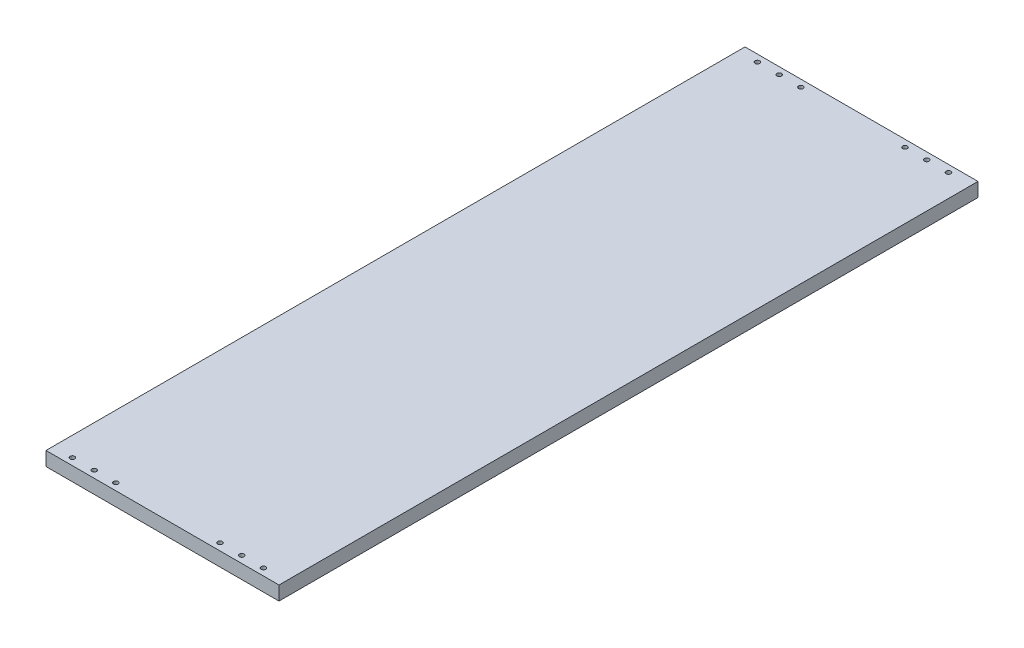
SolidWorks part; units mm, degrees
ref_plane "Спереди" through (0, 0, 0) normal (0, 0, 1) x (1, 0, 0)
ref_plane "Сверху" through (0, 0, 0) normal (0, 1, 0) x (1, 0, 0)
ref_plane "Справа" through (0, 0, 0) normal (1, 0, 0) x (0, 0, -1)
sketch "Эскиз2" plane through (0, 0, 0) normal (0, 1, 0) x (1, 0, 0)
  line L1 (0, 0) -> (300, 0)
  line L2 (0, 0) -> (0, 900)
  line L3 (0, 900) -> (300, 900)
  line L4 (300, 0) -> (300, 900)
extrude "Бобышка-Вытянуть1" add sketch "Эскиз2" along normal blind 18
sketch "Эскиз3" plane through (0, 18, 0) normal (0, 1, 0) x (1, 0, 0)
  line L0 (0, 450) -> (537.494, 450) construction
  line L1 (0, 900) -> (0, 0) construction
  circle A0 centre (25, 9) radius 3
  circle A1 centre (53, 9) radius 3
  circle A2 centre (81, 9) radius 3
  circle A3 centre (215, 9) radius 3
  circle A4 centre (243, 9) radius 3
  circle A5 centre (271, 9) radius 3
  circle A18 centre (271, 891) radius 3
  circle A19 centre (243, 891) radius 3
  circle A20 centre (215, 891) radius 3
  circle A21 centre (81, 891) radius 3
  circle A22 centre (53, 891) radius 3
  circle A23 centre (25, 891) radius 3
  dimension "D1" = 3
  dimension "D2" = 2
extrude "Вырез-Вытянуть1" cut sketch "Эскиз3" against normal blind 9
